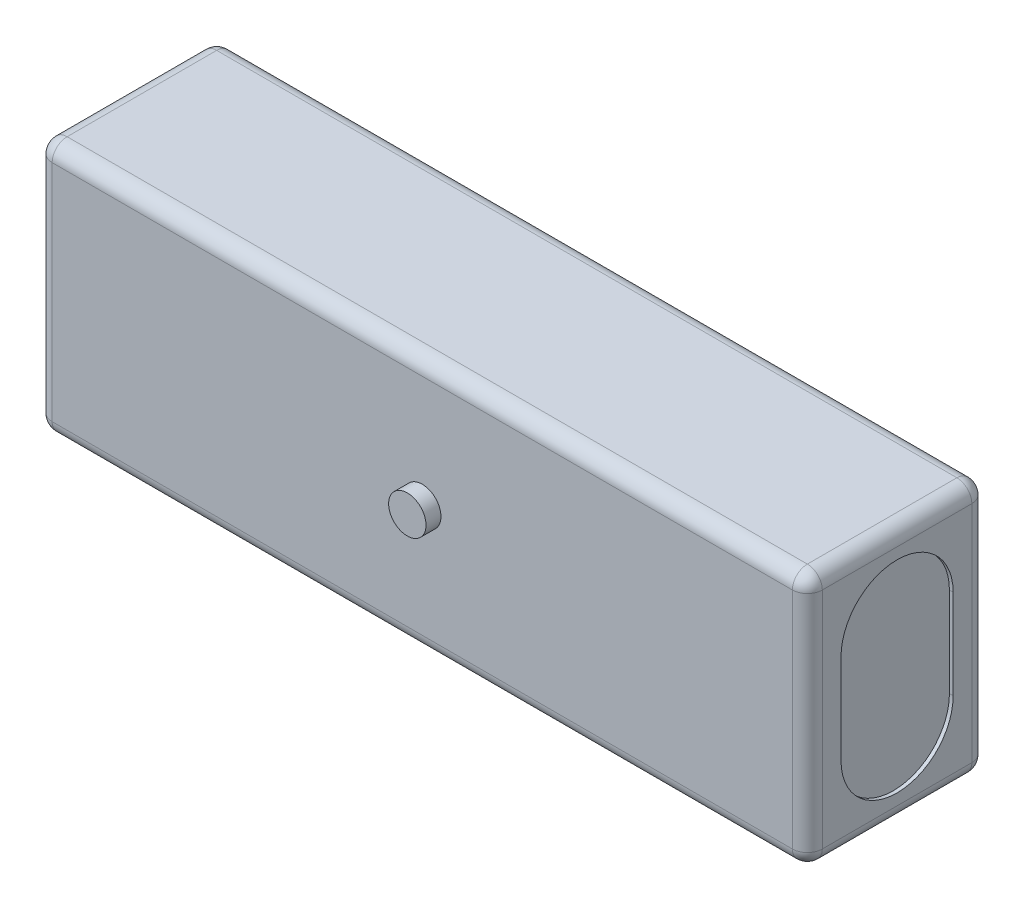
SolidWorks part; units mm, degrees
ref_plane "Plano frontal" through (0, 0, 0) normal (0, 0, 1) x (1, 0, 0)
ref_plane "Plano superior" through (0, 0, 0) normal (0, 1, 0) x (1, 0, 0)
ref_plane "Plano direito" through (0, 0, 0) normal (1, 0, 0) x (0, 0, -1)
sketch "Esboço1" plane through (0, 0, 0) normal (0, 0, 1) x (1, 0, 0)
  line L1 (-51.5, 17) -> (51.5, 17)
  line L2 (-51.5, 17) -> (-51.5, -17)
  line L3 (-51.5, -17) -> (51.5, -17)
  line L4 (51.5, 17) -> (51.5, -17)
  line L5 (-51.5, 17) -> (51.5, -17) construction
  line L6 (-51.5, -17) -> (51.5, 17) construction
  point P0 (0, 0)
  dimension "D1" = 103
  dimension "D2" = 34
extrude "Ressalto-extrusão1" add sketch "Esboço1" along normal blind 24
sketch "Esboço2" plane through (51.5, 0, 0) normal (1, 0, 0) x (0, 0, -1)
  line L0 (-12, 17) -> (-12, -17) construction
  line L1 (-24, 17) -> (0, 17) construction
  line L2 (-24, -17) -> (0, -17) construction
  line L3 (0, 0) -> (-24, 0) construction
  line L4 (-24, -17) -> (-24, 17) construction
  line L5 (-12, 6) -> (-12, -6) construction
  line L6 (-4.5, 6) -> (-4.5, -6)
  line L7 (-19.5, 6) -> (-19.5, -6)
  arc A0 (-4.5, 6) -> (-19.5, 6) centre (-12, 6) ccw
  arc A1 (-19.5, -6) -> (-4.5, -6) centre (-12, -6) ccw
  point P13 (-12, 0)
  dimension "D1" = 12
  dimension "D2" = 15
extrude "Corte-extrusão1" cut sketch "Esboço2" against normal blind 0.5
mirror "Espelhar1" about plane through (0, 0, 0) normal (1, 0, 0) of "Corte-extrusão1"
fillet "Filete1" radius 2 12 edges at (-51.5, -17, 12) (51.5, -17, 12) (-51.5, 0, 0) (0, -17, 0) (51.5, 0, 0) (51.5, 17, 12) (-51.5, 17, 12) (0, 17, 0) (0, -17, 24) (-51.5, 0, 24) (0, 17, 24) (51.5, 0, 24)
sketch "Sketch1" plane through (0, 0, 24) normal (0, 0, 1) x (1, 0, 0)
  circle A0 centre (0, 0) radius 2.5
extrude "Boss-Extrude1" add sketch "Sketch1" along normal blind 2
